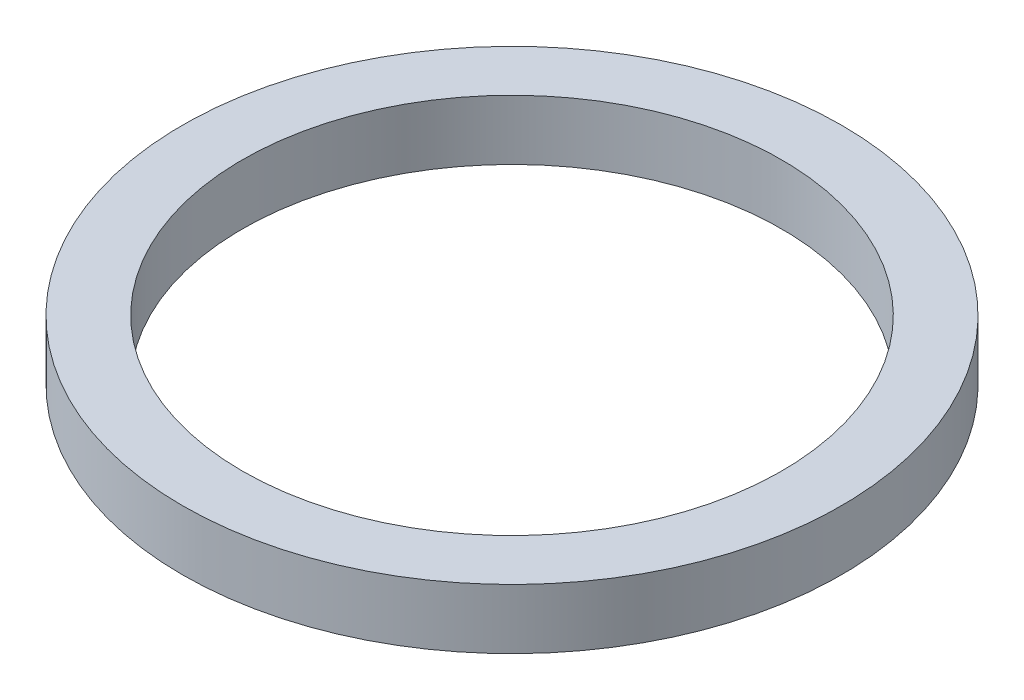
SolidWorks part; units mm, degrees
ref_plane "Face" through (0, 0, 0) normal (0, 0, 1) x (1, 0, 0)
ref_plane "Dessus" through (0, 0, 0) normal (0, 1, 0) x (1, 0, 0)
ref_plane "Droite" through (0, 0, 0) normal (1, 0, 0) x (0, 0, -1)
sketch "Esquisse1" plane through (0, 0, 0) normal (0, 0, 1) x (1, 0, 0)
  line L0 (9, 2.7201) -> (11, 2.7201)
  line L1 (11, 2.7201) -> (11, 0.7201)
  line L2 (11, 0.7201) -> (9, 0.7201)
  line L3 (9, 0.7201) -> (9, 2.7201)
  line L4 (0, 34.1329) -> (0, -20.3069) construction
revolve "Révolution1" add sketch "Esquisse1" angle 360 about L4
